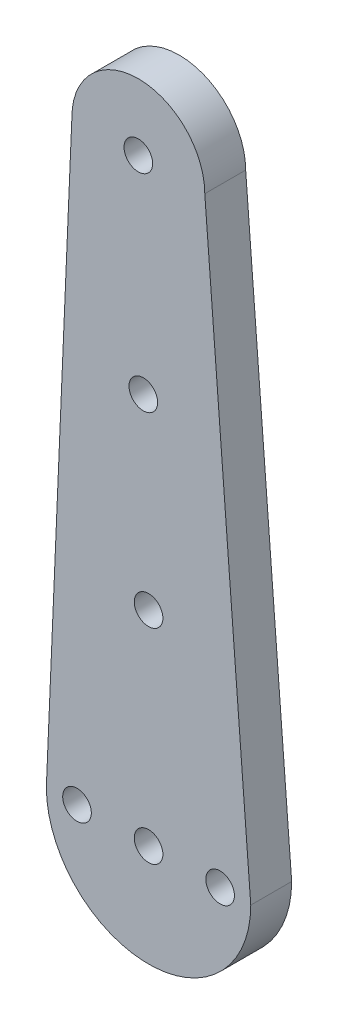
SolidWorks part; units mm, degrees
ref_plane "Front Plane" through (0, 0, 0) normal (0, 0, 1) x (1, 0, 0)
ref_plane "Top Plane" through (0, 0, 0) normal (0, 1, 0) x (1, 0, 0)
ref_plane "Right Plane" through (0, 0, 0) normal (1, 0, 0) x (0, 0, -1)
sketch "Sketch1" plane through (0, 0, 0) normal (0, 0, 1) x (1, 0, 0)
  line L8 (-13.0007, 65.0161) -> (-15.5007, 6.9933)
  line L9 (4.4993, 6.9933) -> (-0.0007, 65.0161)
  line L10 (-5.5007, 6.9933) -> (-5.5007, 17.0657) construction
  arc A0 (-0.0007, 65.0161) -> (-13.0007, 65.0161) centre (-6.5007, 65.0161) ccw
  circle A2 centre (-6.5007, 65.0161) radius 1.4
  circle A3 centre (-5.5007, 6.9933) radius 1.4
  circle A4 centre (-6.0128, 45.0161) radius 1.4
  arc A5 (-15.4636, 7.8535) -> (4.3797, 8.5352) centre (-5.5007, 6.9933) ccw
  circle A6 centre (1.4993, 6.9933) radius 1.4
  circle A7 centre (-12.5007, 6.9933) radius 1.4
  circle A8 centre (-5.5007, 26.9933) radius 1.4
  point P8 (-5.0007, 1.5161)
  point P11 (-6.5007, 71.5161)
  dimension "D1" = 13
  dimension "D4" = 2.8
  dimension "D5" = 20
  dimension "D2" = 2.8
  dimension "D3" = 2.8
  dimension "D6" = 2.8
  dimension "D8" = 20
  dimension "D10" = 2.8
  dimension "D7" = 70
  dimension "D9" = 7
  dimension "D11" = 20
extrude "Boss-Extrude1" add sketch "Sketch1" along normal blind 4
